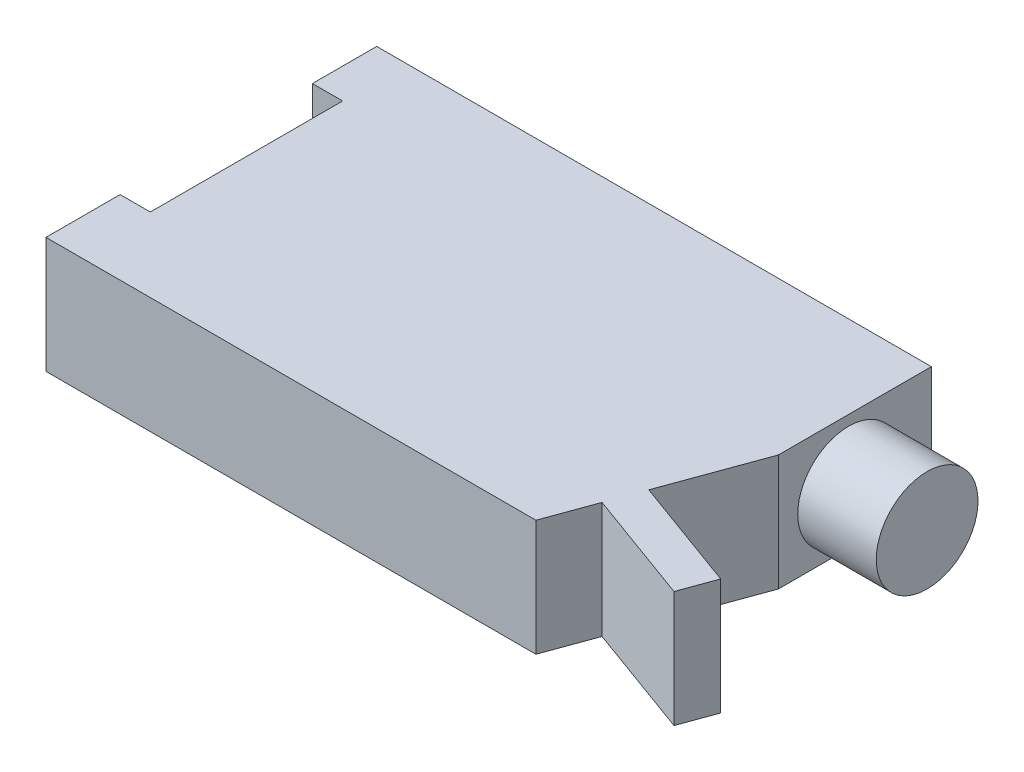
SolidWorks part; units mm, degrees
ref_plane "Front Plane" through (0, 0, 0) normal (0, 0, 1) x (1, 0, 0)
ref_plane "Top Plane" through (0, 0, 0) normal (0, 1, 0) x (1, 0, 0)
ref_plane "Right Plane" through (0, 0, 0) normal (1, 0, 0) x (0, 0, -1)
sketch "Sketch1" plane through (0, 0, 0) normal (0, 1, 0) x (1, 0, 0)
  line L0 (37.063, 27.0754) -> (37.063, 0.7329)
  line L1 (-58.4732, 27.0754) -> (37.063, 27.0754)
  line L2 (-58.4732, 27.0754) -> (-58.4732, -29.8884)
  line L3 (-58.4732, -29.8884) -> (25.9177, -29.8884)
  line L5 (37.063, 0.7329) -> (31.1048, -15.6369)
  line L6 (28.9563, -21.54) -> (48.4426, -28.6324)
  line L7 (48.4426, -28.6324) -> (50.5911, -22.7294)
  line L8 (50.5911, -22.7294) -> (31.1048, -15.6369)
  line L9 (28.9563, -21.54) -> (25.9177, -29.8884)
  dimension "D1" = 70
extrude "Boss-Extrude1" add sketch "Sketch1" along normal blind 20
sketch "Sketch2" plane through (37.063, 0, 0) normal (1, 0, 0) x (0, 0, -1)
  circle A0 centre (12.8217, 9.4804) radius 8.7622
extrude "Boss-Extrude2" add sketch "Sketch2" along normal up to vertex (13.5282 mm away) up to point (50.5911, 0, 22.7294)
sketch "Sketch3" plane through (0, 20, 0) normal (0, 1, 0) x (1, 0, 0)
  line L0 (-58.4732, 27.0754) -> (-58.4732, -29.8884) construction
  line L1 (-53.2723, -17.1273) -> (-58.4732, -17.1273)
  line L2 (-53.2723, -17.1273) -> (-53.2723, 16.0011)
  line L3 (-53.2723, 16.0011) -> (-58.4732, 16.0011)
  line L4 (-58.4732, -17.1273) -> (-58.4732, 16.0011)
extrude "Cut-Extrude1" cut sketch "Sketch3" against normal through all
